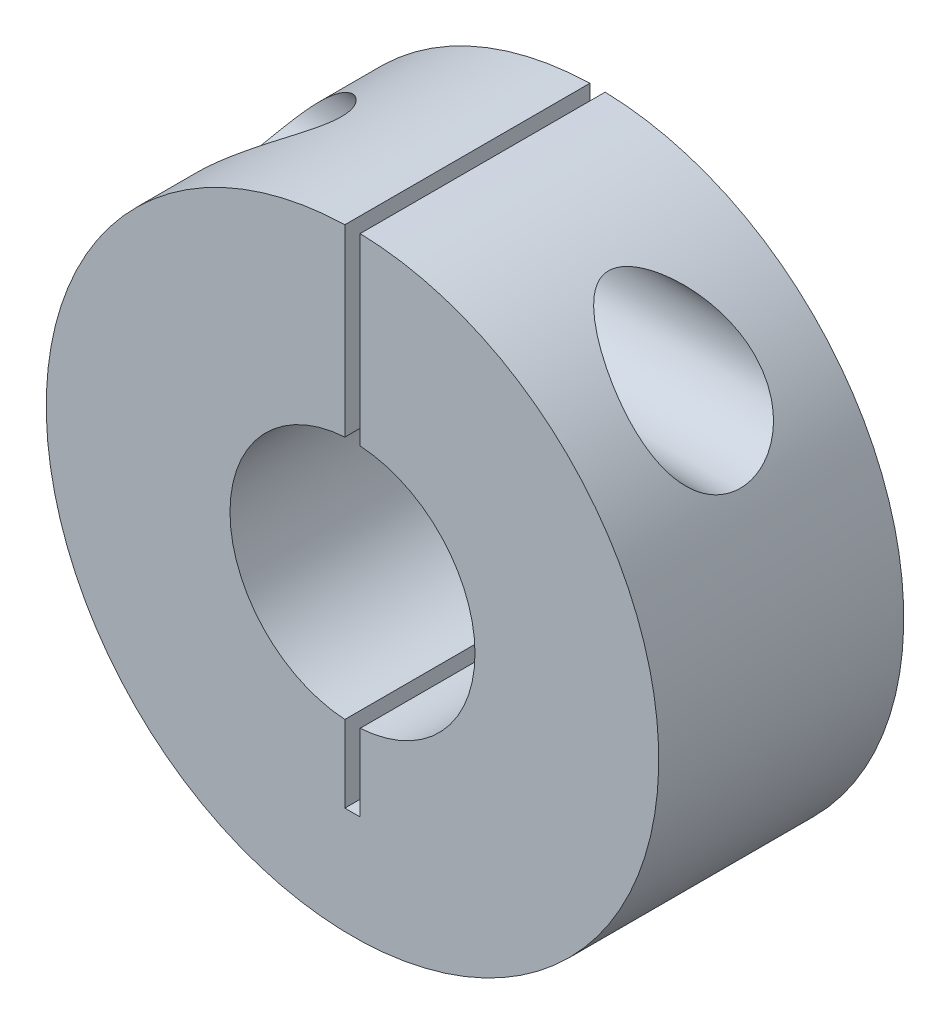
SolidWorks part; units mm, degrees
ref_plane "Front Plane" through (0, 0, 0) normal (0, 0, 1) x (1, 0, 0)
ref_plane "Top Plane" through (0, 0, 0) normal (0, 1, 0) x (1, 0, 0)
ref_plane "Right Plane" through (0, 0, 0) normal (1, 0, 0) x (0, 0, -1)
sketch "Sketch1" plane through (0, 0, 0) normal (0, 0, 1) x (1, 0, 0)
  circle A0 centre (0, 0) radius 4
  circle A1 centre (0, 0) radius 10
  dimension "D1" = 8
  dimension "D2" = 20
extrude "Boss-Extrude1" add sketch "Sketch1" along normal blind 8
sketch "Sketch2" plane through (0, 0, 8) normal (0, 0, 1) x (1, 0, 0)
  line L1 (-0.25, -6.5) -> (0.25, -6.5)
  line L2 (-0.25, -6.5) -> (-0.25, 10.5)
  line L3 (-0.25, 10.5) -> (0.25, 10.5)
  line L4 (0.25, -6.5) -> (0.25, 10.5)
  line L5 (-0.25, -6.5) -> (0.25, 10.5) construction
  line L6 (-0.25, 10.5) -> (0.25, -6.5) construction
  point P0 (0, 2)
  point P5 (0, 0)
  point P7 (0, 0)
  dimension "D1" = 17
  dimension "D3" = 0.5
  dimension "D4" = 10.5
extrude "Cut-Extrude1" cut sketch "Sketch2" against normal blind 8
sketch "Sketch3" plane through (0, 0, 0) normal (1, 0, 0) x (0, 0, -1)
  circle A0 centre (-4, 7) radius 2
  dimension "D2" = 4
  dimension "D1" = 4
  dimension "D3" = 7
extrude "Cut-Extrude2" cut sketch "Sketch3" against normal through all both and the other way through all
